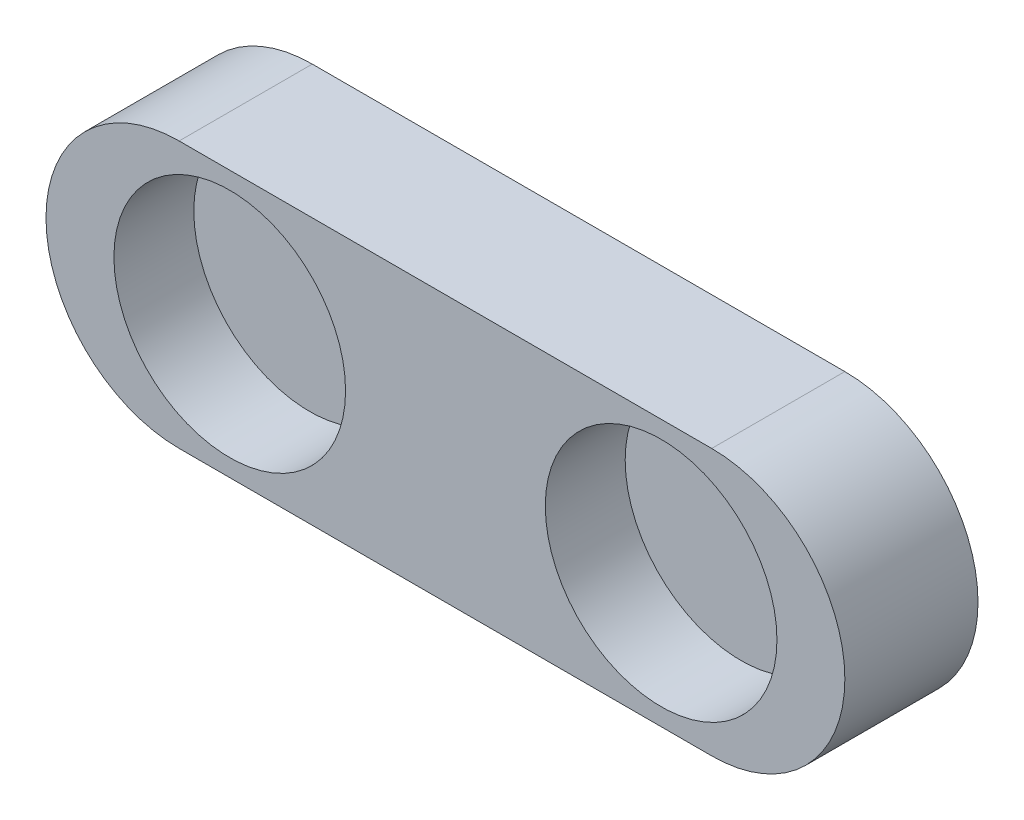
SolidWorks part; units mm, degrees
ref_plane "Front Plane" through (0, 0, 0) normal (0, 0, 1) x (1, 0, 0)
ref_plane "Top Plane" through (0, 0, 0) normal (0, 1, 0) x (1, 0, 0)
ref_plane "Right Plane" through (0, 0, 0) normal (1, 0, 0) x (0, 0, -1)
sketch "Sketch1" plane through (0, 0, 0) normal (0, 0, 1) x (1, 0, 0)
  line L1 (0, 0) -> (50.8, 0)
  line L3 (0, 25.4) -> (50.8, 25.4)
  arc A0 (0, 25.4) -> (0, 0) centre (0, 12.7) ccw
  arc A1 (50.8, 0) -> (50.8, 25.4) centre (50.8, 12.7) ccw
  dimension "D2" = 12.7
  dimension "D3" = 12.7
  dimension "D1" = 25.4
  dimension "D4" = 50.8
extrude "Boss-Extrude1" add sketch "Sketch1" along normal blind 12.7
sketch "Sketch2" plane through (0, 0, 12.7) normal (0, 0, 1) x (1, 0, 0)
  line L0 (0, 0) -> (50.8, 0) construction
  circle A0 centre (4.826, 12.7) radius 11.049
  circle A1 centre (45.974, 12.7) radius 11.049
  point P6 (25.4, 0)
  dimension "D1" = 22.098
  dimension "D2" = 22.098
  dimension "D3" = 12.7
  dimension "D4" = 12.7
  dimension "D5" = 41.148
  dimension "D6" = 20.574
extrude "Cut-Extrude1" cut sketch "Sketch2" against normal blind 7.62
